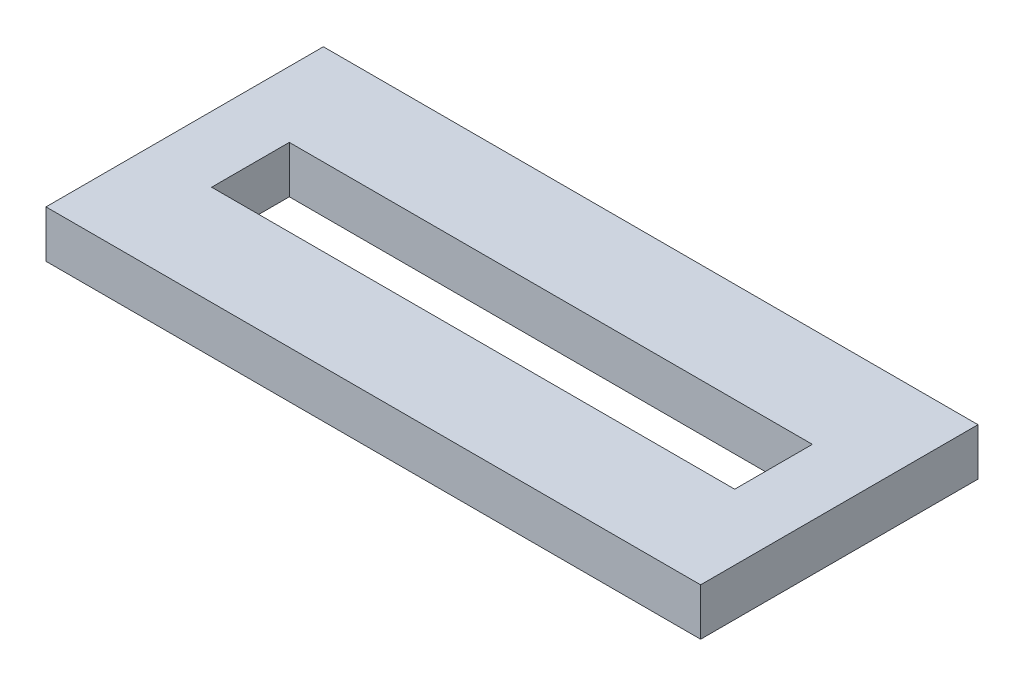
SolidWorks part; units mm, degrees
ref_plane "Front Plane" through (0, 0, 0) normal (0, 0, 1) x (1, 0, 0)
ref_plane "Top Plane" through (0, 0, 0) normal (0, 1, 0) x (1, 0, 0)
ref_plane "Right Plane" through (0, 0, 0) normal (1, 0, 0) x (0, 0, -1)
sketch "Sketch2" plane through (0, 0, 0) normal (0, 1, 0) x (1, 0, 0)
  line L1 (-36.0469, 10.1719) -> (22.9531, 10.1719)
  line L2 (-36.0469, 10.1719) -> (-36.0469, -14.8281)
  line L3 (-36.0469, -14.8281) -> (22.9531, -14.8281)
  line L4 (22.9531, 10.1719) -> (22.9531, -14.8281)
  dimension "D1" = 59
  dimension "D2" = 25
extrude "Boss-Extrude1" add sketch "Sketch2" along normal blind 4.25
sketch "Sketch3" plane through (0, 4.25, 0) normal (0, 1, 0) x (1, 0, 0)
  line L1 (-30.1178, 1.1719) -> (17.024, 1.1719)
  line L2 (-30.1178, 1.1719) -> (-30.1178, -5.8281)
  line L3 (-30.1178, -5.8281) -> (17.024, -5.8281)
  line L4 (17.024, 1.1719) -> (17.024, -5.8281)
  line L5 (22.9531, 10.1719) -> (-36.0469, 10.1719) construction
  line L6 (-36.0469, -14.8281) -> (22.9531, -14.8281) construction
  line L7 (-6.5469, -14.8281) -> (-6.5469, 10.1719) construction
  point P4 (-6.5469, 1.1719)
  dimension "D1" = 9
  dimension "D2" = 9
extrude "Cut-Extrude1" cut sketch "Sketch3" against normal through all
